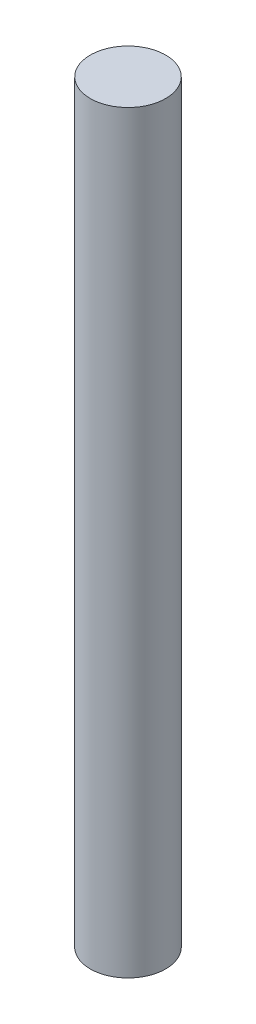
SolidWorks part; units mm, degrees
material "Plain Carbon Steel"
ref_plane "Front Plane" through (0, 0, 0) normal (0, 0, 1) x (1, 0, 0)
ref_plane "Top Plane" through (0, 0, 0) normal (0, 1, 0) x (1, 0, 0)
ref_plane "Right Plane" through (0, 0, 0) normal (1, 0, 0) x (0, 0, -1)
sketch "Sketch1" plane through (0, 0, 0) normal (0, 1, 0) x (1, 0, 0)
  circle A0 centre (0, 0) radius 3.175
extrude "Boss-Extrude1" add sketch "Sketch1" along normal mid plane 63.5
